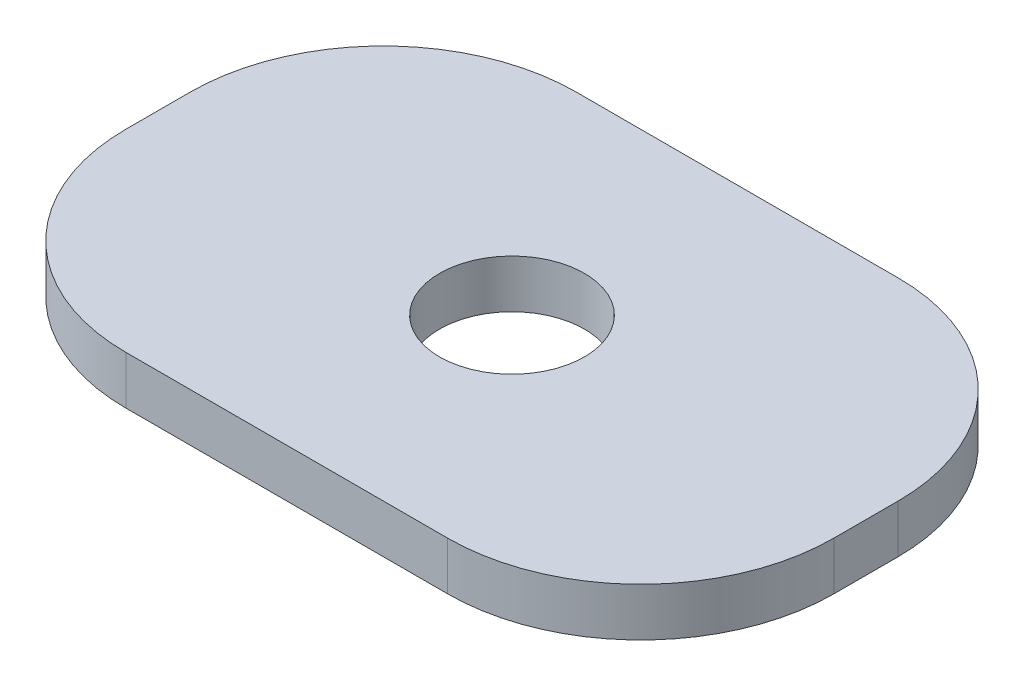
SolidWorks part; units mm, degrees
ref_plane "Front Plane" through (0, 0, 0) normal (0, 0, 1) x (1, 0, 0)
ref_plane "Top Plane" through (0, 0, 0) normal (0, 1, 0) x (1, 0, 0)
ref_plane "Right Plane" through (0, 0, 0) normal (1, 0, 0) x (0, 0, -1)
sketch "Sketch1" plane through (0, 0, 0) normal (0, 1, 0) x (1, 0, 0)
  line L1 (-34.925, -22.225) -> (34.925, -22.225)
  line L2 (-34.925, -22.225) -> (-34.925, 22.225)
  line L3 (-34.925, 22.225) -> (34.925, 22.225)
  line L4 (34.925, -22.225) -> (34.925, 22.225)
  line L5 (-34.925, -22.225) -> (34.925, 22.225) construction
  line L6 (-34.925, 22.225) -> (34.925, -22.225) construction
  point P0 (0, 0)
  dimension "D1" = 44.45
  dimension "D2" = 69.85
extrude "Boss-Extrude1" add sketch "Sketch1" along normal blind 4.7625
sketch "Sketch2" plane through (0, 4.7625, 0) normal (0, 1, 0) x (1, 0, 0)
  line L0 (-34.925, 22.225) -> (-34.925, -22.225) construction
  circle A0 centre (0, 0) radius 7.1438
  point P0 (0, 0)
  point P5 (0, 0)
  point P6 (-34.925, 0)
  dimension "D1" = 14.2875
  dimension "D2" = 34.925
extrude "Cut-Extrude1" cut sketch "Sketch2" against normal through all
fillet "Fillet1" radius 19.05 2 edges at (-34.925, 2.3813, -22.225) (-34.925, 2.3813, 22.225)
fillet "Fillet2" radius 19.05 2 edges at (34.925, 2.3813, 22.225) (34.925, 2.3813, -22.225)
